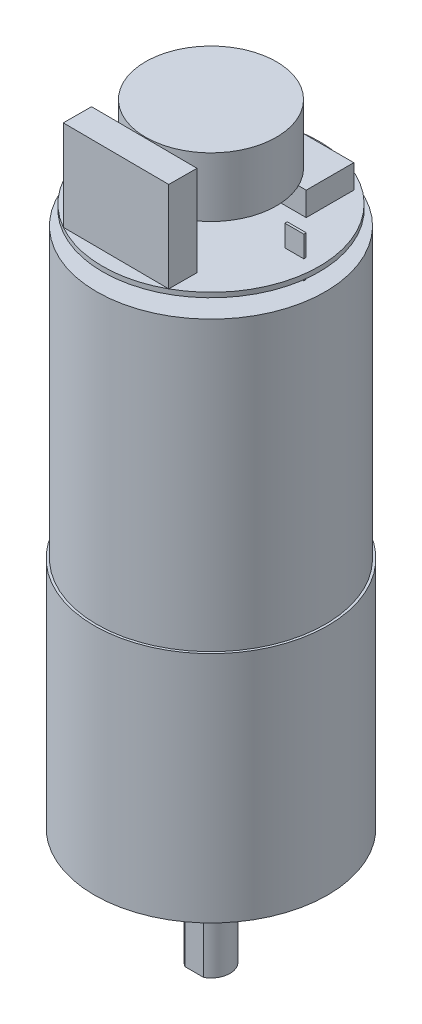
SolidWorks part; units mm, degrees
ref_plane "Front Plane" through (0, 0, 0) normal (0, 0, 1) x (1, 0, 0)
ref_plane "Top Plane" through (0, 0, 0) normal (0, 1, 0) x (1, 0, 0)
ref_plane "Right Plane" through (0, 0, 0) normal (1, 0, 0) x (0, 0, -1)
sketch "Sketch1" plane through (0, 0, 0) normal (0, 1, 0) x (1, 0, 0)
  line L0 (0, 12.446) -> (0, -12.446) construction
  line L1 (-12.446, 0) -> (12.446, 0) construction
  line L2 (-12.446, 0) -> (-9.017, 0) construction
  line L3 (9.017, 0) -> (12.446, 0) construction
  circle A0 centre (0, 0) radius 12.446
  circle A1 centre (-9.017, 0) radius 1.27
  circle A2 centre (9.017, 0) radius 1.27
  dimension "D1" = 24.892
  dimension "D3" = 2.54
  dimension "D4" = 2.54
  dimension "D2" = 18.034
extrude "Boss-Extrude1" add sketch "Sketch1" along normal blind 24.892
sketch "Sketch2" plane through (0, 24.892, 0) normal (0, 1, 0) x (1, 0, 0)
  line L0 (0, 12.446) -> (0, -12.446) construction
  line L1 (-12.446, 0) -> (12.446, 0) construction
  circle A0 centre (0, 0) radius 12.446 construction
hole_wizard "CSK for M3 Flat Head Machine Screw1" positions "Sketch3" profile "Sketch4" countersink size "M3" standard "ANSI Metric" end condition through all
sketch "Sketch3" plane through (0, 24.892, 0) normal (0, 1, 0) x (1, 0, 0)
  line L0 (0, 12.446) -> (0, -12.446) construction
  point P1 (0, 8.1199)
  point P5 (0, -7.587)
sketch "Sketch4" plane through (0, 24.892, -8.1199) normal (1, 0, 0) x (0, 0, 1)
  line L0 (0, 0) -> (0, 24.892)
  line L1 (0, 24.892) -> (1.7, 24.892)
  line L2 (1.7, 24.892) -> (1.7, 1.45)
  line L3 (1.7, 1.45) -> (3.15, 0)
  line L5 (3.15, 0) -> (0, 0)
  line L6 (-1.7, 1.45) -> (-3.15, 0) construction
  line L11 (0, -6.35) -> (0, 107.95) construction
  dimension "Thru Hole Dia." = 3.4
  dimension "Thru Hole Depth" = 24.892
  dimension "Near C'Sink Dia." = 6.3
  dimension "Near C'Sink Angle" = 90
ref_plane "Plane1" through (0, 24.892, 0) normal (0, 1, 0) x (1, 0, 0)
sketch "Sketch5" plane through (0, 24.892, 0) normal (0, 1, 0) x (1, 0, 0)
  circle A0 centre (0, 0) radius 12.192
  dimension "D1" = 24.384
extrude "Boss-Extrude2" add sketch "Sketch5" along normal blind 30.734
sketch "Sketch6" plane through (0, 0, 0) normal (0, 1, 0) x (1, 0, 0)
  circle A0 centre (0, 0) radius 3.556
  dimension "D1" = 7.112
extrude "Boss-Extrude3" add sketch "Sketch6" against normal blind 2.54
ref_plane "Plane2" through (0, -2.54, 0) normal (0, -1, 0) x (-1, 0, 0)
sketch "Sketch7" plane through (0, -2.54, 0) normal (0, -1, 0) x (-1, 0, 0)
  circle A0 centre (0, 0) radius 2.032
  dimension "D1" = 4.064
extrude "Boss-Extrude4" add sketch "Sketch7" along normal blind 9.906
ref_plane "Plane3" through (0, -12.446, 0) normal (0, -1, 0) x (-1, 0, 0)
sketch "Sketch8" plane through (0, -12.446, 0) normal (0, -1, 0) x (-1, 0, 0)
  line L0 (0, 12.446) -> (0, -12.446) construction
  line L1 (-1.016, -1.778) -> (1.016, -1.778)
  line L2 (-1.016, -1.778) -> (-1.016, -2.032)
  line L3 (-1.016, -2.032) -> (1.016, -2.032)
  line L4 (1.016, -1.778) -> (1.016, -2.032)
  line L5 (-1.016, -1.778) -> (1.016, -2.032) construction
  line L6 (-1.016, -2.032) -> (1.016, -1.778) construction
  line L7 (12.446, 0) -> (-12.446, 0) construction
  line L8 (-2.032, 0) -> (2.032, 0) construction
  line L9 (-1.016, 2.032) -> (1.016, 2.032)
  line L10 (1.016, 1.778) -> (1.016, 2.032)
  line L11 (-1.016, 1.778) -> (1.016, 1.778)
  line L12 (-1.016, 1.778) -> (-1.016, 2.032)
  circle A0 centre (0, 0) radius 2.032 construction
  point P0 (0, -1.905)
  dimension "D1" = 0.254
  dimension "D2" = 1.778
  dimension "D3" = 2.032
extrude "Cut-Extrude2" cut sketch "Sketch8" against normal blind 9.906
ref_plane "Plane4" through (0, 55.626, 0) normal (0, 1, 0) x (1, 0, 0)
sketch "Sketch9" plane through (0, 55.626, 0) normal (0, 1, 0) x (1, 0, 0)
  circle A0 centre (0, 0) radius 3.175
  dimension "D1" = 6.35
extrude "Boss-Extrude5" add sketch "Sketch9" along normal blind 1.524
sketch "Sketch10" plane through (0, 55.626, 0) normal (0, 1, 0) x (1, 0, 0)
  line L0 (0, 12.446) -> (0, -12.446) construction
  line L1 (-12.446, 0) -> (12.446, 0) construction
  line L2 (-10.033, -0.127) -> (-8.001, -0.127)
  line L3 (-10.033, -0.127) -> (-10.033, 0.127)
  line L4 (-10.033, 0.127) -> (-8.001, 0.127)
  line L5 (-8.001, -0.127) -> (-8.001, 0.127)
  line L6 (-10.033, -0.127) -> (-8.001, 0.127) construction
  line L7 (-10.033, 0.127) -> (-8.001, -0.127) construction
  line L8 (-12.192, 0) -> (-10.033, 0) construction
  line L9 (10.033, -0.127) -> (8.001, -0.127)
  line L10 (10.033, -0.127) -> (10.033, 0.127)
  line L11 (10.033, 0.127) -> (8.001, 0.127)
  line L12 (8.001, -0.127) -> (8.001, 0.127)
  line L13 (10.033, -0.127) -> (8.001, 0.127) construction
  line L14 (10.033, 0.127) -> (8.001, -0.127) construction
  line L15 (10.033, 0) -> (12.192, 0) construction
  circle A0 centre (0, 0) radius 12.192 construction
  point P4 (-9.017, 0)
  point P11 (9.017, 0)
  dimension "D1" = 18.034
  dimension "D2" = 2.032
  dimension "D3" = 0.254
  dimension "D4" = 2.032
  dimension "D5" = 0.254
extrude "Boss-Extrude6" add sketch "Sketch10" along normal blind 4.318
ref_plane "Plane5" through (0, 57.15, 0) normal (0, 1, 0) x (1, 0, 0)
sketch "Sketch11" plane through (0, 57.15, 0) normal (0, 1, 0) x (1, 0, 0)
  line L1 (-10.033, -0.127) -> (-8.001, -0.127)
  line L2 (-10.033, -0.127) -> (-10.033, 0.127)
  line L3 (-10.033, 0.127) -> (-8.001, 0.127)
  line L4 (-8.001, -0.127) -> (-8.001, 0.127)
  line L5 (8.001, -0.127) -> (10.033, -0.127)
  line L6 (8.001, -0.127) -> (8.001, 0.127)
  line L7 (8.001, 0.127) -> (10.033, 0.127)
  line L8 (10.033, -0.127) -> (10.033, 0.127)
  circle A0 centre (0, 0) radius 11.557
  dimension "D1" = 23.114
extrude "Boss-Extrude7" add sketch "Sketch11" along normal blind 0.508
ref_plane "Plane6" through (0, 57.658, 0) normal (0, 1, 0) x (1, 0, 0)
sketch "Sketch12" plane through (0, 57.658, 0) normal (0, 1, 0) x (1, 0, 0)
  line L0 (0, 12.446) -> (0, -12.446) construction
  line L1 (6.35, 3.81) -> (-6.35, 3.81)
  line L2 (6.35, 3.81) -> (6.35, 8.89)
  line L3 (6.35, 8.89) -> (-6.35, 8.89)
  line L4 (-6.35, 3.81) -> (-6.35, 8.89)
  line L5 (6.35, 3.81) -> (-6.35, 8.89) construction
  line L6 (6.35, 8.89) -> (-6.35, 3.81) construction
  point P0 (0, 6.35)
  dimension "D1" = 6.35
  dimension "D2" = 5.08
  dimension "D3" = 12.7
extrude "Boss-Extrude8" add sketch "Sketch12" along normal blind 2.54
sketch "Sketch13" plane through (0, 57.658, 0) normal (0, 1, 0) x (1, 0, 0)
  line L1 (1.905, -1.27) -> (-1.905, -1.27)
  line L2 (1.905, -1.27) -> (1.905, 1.27)
  line L3 (1.905, 1.27) -> (-1.905, 1.27)
  line L4 (-1.905, -1.27) -> (-1.905, 1.27)
  line L5 (1.905, -1.27) -> (-1.905, 1.27) construction
  line L6 (1.905, 1.27) -> (-1.905, -1.27) construction
  point P0 (0, 0)
  point P6 (-1.905, 0)
  dimension "D1" = 3.81
  dimension "D2" = 2.54
extrude "Boss-Extrude9" add sketch "Sketch13" along normal blind 2.794
sketch "Sketch14" plane through (0, 57.658, 0) normal (0, 1, 0) x (1, 0, 0)
  line L0 (-5.7185, -10.0431) -> (5.5974, -10.1111)
  line L1 (-5.7185, -10.0431) -> (-5.7005, -7.0428)
  line L2 (5.5974, -10.1111) -> (5.6154, -7.1108)
  line L3 (-5.7005, -7.0428) -> (5.6154, -7.1108)
  circle A0 centre (0, 0) radius 11.557 construction
  dimension "D1" = 11.3159
  dimension "D2" = 3.0003
  dimension "D3" = 2.3685
extrude "Boss-Extrude10" add sketch "Sketch14" along normal blind 9.652
ref_plane "Plane7" through (0, 60.452, 0) normal (0, 1, 0) x (1, 0, 0)
sketch "Sketch15" plane through (0, 60.452, 0) normal (0, 1, 0) x (1, 0, 0)
  circle A0 centre (0, 0) radius 3.175
  dimension "D1" = 6.35
extrude "Boss-Extrude11" add sketch "Sketch15" along normal blind 0.508
ref_plane "Plane8" through (0, 60.96, 0) normal (0, 1, 0) x (1, 0, 0)
sketch "Sketch16" plane through (0, 60.96, 0) normal (0, 1, 0) x (1, 0, 0)
  circle A0 centre (0, 0) radius 6.985
  dimension "D1" = 13.97
extrude "Boss-Extrude12" add sketch "Sketch16" along normal blind 6.35
equation "\"big diameter\" = .98in"
equation "\"screw distance\"= 0.71in"
equation "\"small cross holes\"= 0.10in"
